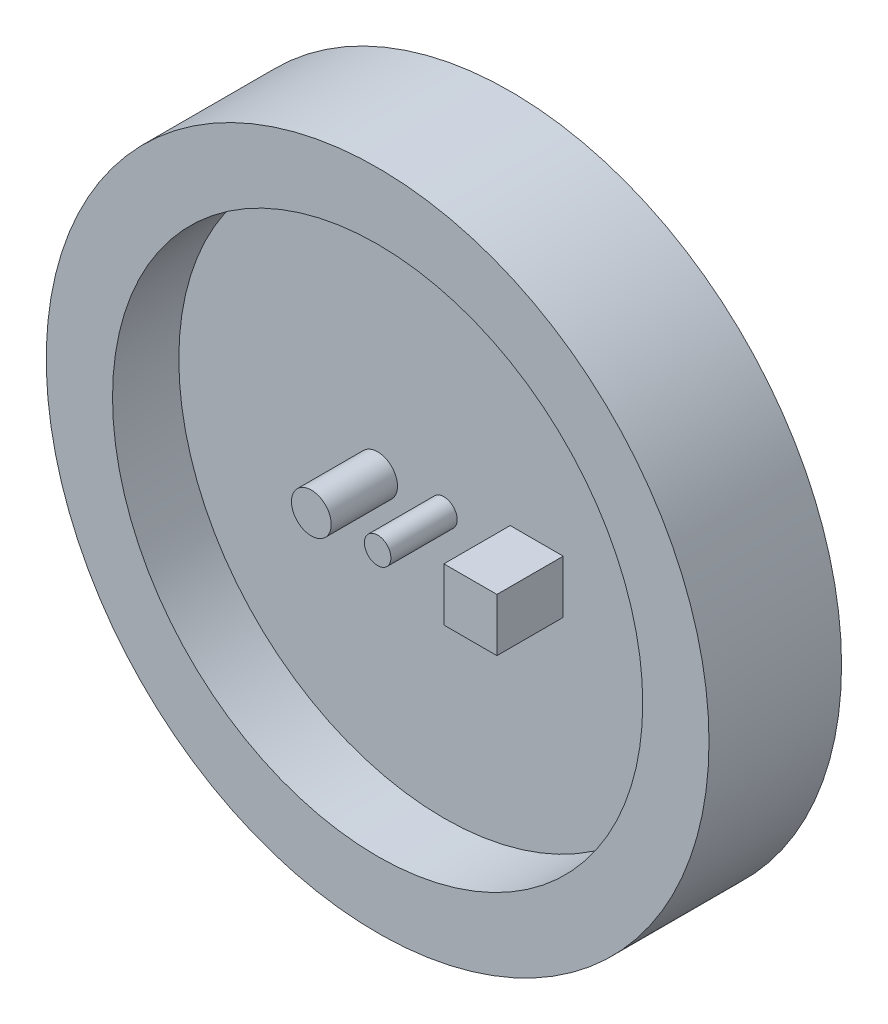
SolidWorks part; units mm, degrees
ref_plane "Front Plane" through (0, 0, 0) normal (0, 0, 1) x (1, 0, 0)
ref_plane "Top Plane" through (0, 0, 0) normal (0, 1, 0) x (1, 0, 0)
ref_plane "Right Plane" through (0, 0, 0) normal (1, 0, 0) x (0, 0, -1)
sketch "Sketch1" plane through (0, 0, 0) normal (0, 0, 1) x (1, 0, 0)
  circle A0 centre (0, 0) radius 25
  dimension "D1" = 50
extrude "Boss-Extrude1" add sketch "Sketch1" along normal blind 10
shell "Shell3" thickness 5
sketch "Sketch3" plane through (0, 0, 5) normal (0, 0, 1) x (1, 0, 0)
  line L0 (19.1198, 0) -> (20, 0) construction
  line L1 (5, -2.3812) -> (9, -2.3812)
  line L2 (5, -2.3812) -> (5, 1.6188)
  line L3 (5, 1.6188) -> (9, 1.6188)
  line L4 (9, -2.3812) -> (9, 1.6188)
  line L5 (20, 0) -> (-20, 0) construction
  circle A0 centre (-5, -0.0611) radius 1.5
  circle A1 centre (0, 0) radius 1
  circle A2 centre (0, 0) radius 20 construction
  dimension "D1" = 3
  dimension "D4" = 2
  dimension "D5" = 5
  dimension "D6" = 5
  dimension "D2" = 4
  dimension "D3" = 4
extrude "Boss-Extrude2" add sketch "Sketch3" along normal blind 5
